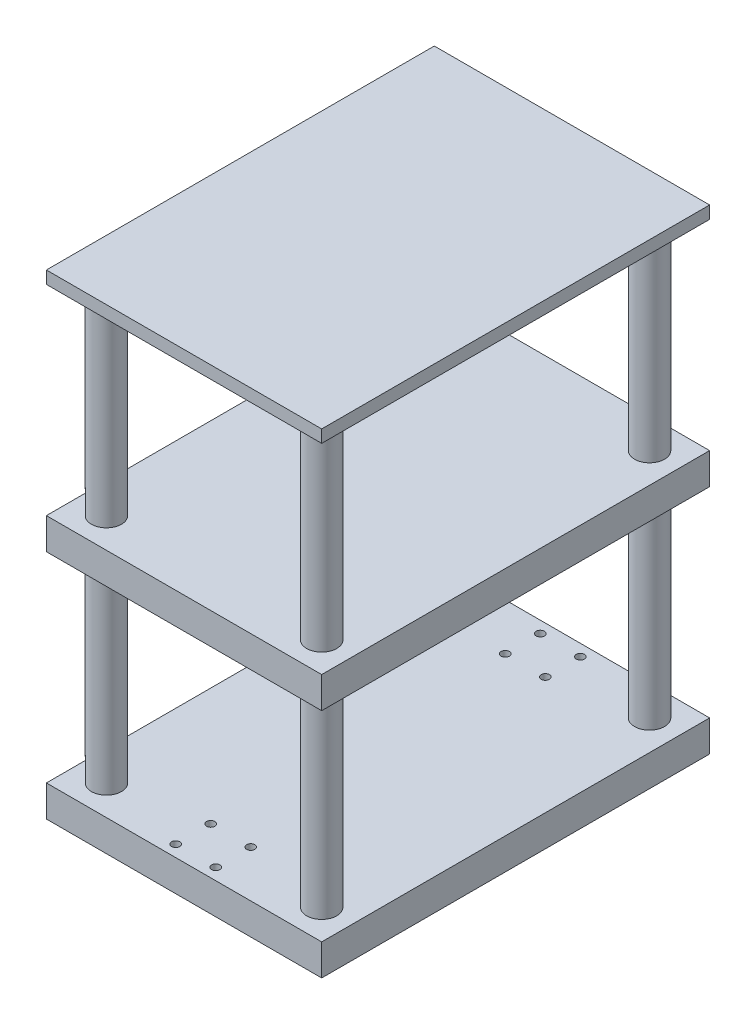
SolidWorks part; units mm, degrees
material "Custom Plastic"
ref_plane "Front Plane" through (0, 0, 0) normal (0, 0, 1) x (1, 0, 0)
ref_plane "Top Plane" through (0, 0, 0) normal (0, 1, 0) x (1, 0, 0)
ref_plane "Right Plane" through (0, 0, 0) normal (1, 0, 0) x (0, 0, -1)
sketch "Sketch1" plane through (0, 0, 0) normal (0, 1, 0) x (1, 0, 0)
  line L1 (-55, 77.5) -> (55, 77.5)
  line L2 (-55, 77.5) -> (-55, -77.5)
  line L3 (-55, -77.5) -> (55, -77.5)
  line L4 (55, 77.5) -> (55, -77.5)
  line L5 (-55, 77.5) -> (55, -77.5) construction
  line L6 (-55, -77.5) -> (55, 77.5) construction
  point P0 (0, 0)
  dimension "D1" = 155
  dimension "D2" = 110
extrude "Boss-Extrude1" add sketch "Sketch1" along normal blind 12.5
sketch "Sketch2" plane through (0, 12.5, 0) normal (0, 1, 0) x (1, 0, 0)
  line L0 (-55, 77.5) -> (-55, -77.5) construction
  line L1 (55, 77.5) -> (-55, 77.5) construction
  line L2 (0, 0) -> (73.1979, 0) construction
  circle A0 centre (-43, 65.5) radius 6
  dimension "D1" = 12
  dimension "D2" = 12
  dimension "D3" = 12
extrude "Boss-Extrude2" add sketch "Sketch2" along normal blind 80 contours A0
mirror "Mirror1" about plane through (0, 0, 0) normal (0, 0, 1) of "Boss-Extrude2"
mirror "Mirror2" about plane through (0, 0, 0) normal (1, 0, 0) of "Mirror1", "Boss-Extrude2"
ref_plane "Plane1" through (0, 92.5, 0) normal (0, 1, 0) x (1, 0, 0)
pattern_linear "LPattern1" count 2 spacing 92.5 along (0, -1, 0) of bodies 104
pattern_linear "LPattern2" [suppressed] count 2 spacing 92.5
sketch "Sketch4" plane through (0, -92.5, 0) normal (0, -1, 0) x (1, 0, 0)
  line L0 (0, 77.5) -> (0, 74.5)
  line L1 (-55, 77.5) -> (55, 77.5) construction
  line L2 (-13.25, 74.5) -> (13.25, 74.5)
  line L4 (-13.25, 74.5) -> (-13.25, 72.85)
  line L5 (-13.25, 72.85) -> (13.25, 72.85)
  line L6 (13.25, 72.85) -> (13.25, 74.5)
  circle A0 centre (-8, 72.85) radius 1.65
  circle A1 centre (8, 72.85) radius 1.65
  dimension "D1" = 3.3
  dimension "D2" = 3.3
  dimension "D3" = 16
  dimension "D4" = 26.5
  dimension "D5" = 5.25
  dimension "D6" = 5.25
  dimension "D7" = 1.65
  dimension "D8" = 3
sketch "Sketch5" plane through (0, -92.5, 0) normal (0, -1, 0) x (-1, 0, 0)
  point P0 (-8, -72.85)
  point P3 (8, -72.85)
hole_wizard "Ø3.3 (3.3) Diameter Hole1" positions "Sketch5" profile "Sketch6" hole size "Ø3.3" standard "ISO"
sketch "Sketch6" plane through (8, -92.5, 72.85) normal (1, 0, 0) x (0, 0, -1)
  line L0 (0, 0) -> (0, 20.9914)
  line L1 (0, 20.9914) -> (1.65, 20)
  line L2 (1.65, 20) -> (1.65, 0)
  line L5 (1.65, 0) -> (0, 0)
  line L10 (0, 20.9914) -> (-1.65, 20) construction
  line L11 (0, -6.35) -> (0, 107.95) construction
  dimension "Hole Dia." = 3.3
  dimension "Hole Depth" = 20
  dimension "Drill Angle" = 118
pattern_linear "LPattern3" count 2 spacing 14 along (0, 0, -1) of "Ø3.3 (3.3) Diameter Hole1"
mirror "Mirror3" about plane through (0, 0, 0) normal (0, 0, 1) of "LPattern3", "Ø3.3 (3.3) Diameter Hole1"
sketch "Sketch7" plane through (0, 92.5, 0) normal (0, 1, 0) x (1, 0, 0)
  line L4 (55, -77.5) -> (55, 77.5)
  line L5 (55, 77.5) -> (-55, 77.5)
  line L6 (-55, 77.5) -> (-55, -77.5)
  line L7 (-55, -77.5) -> (55, -77.5)
  line L8 (55, -77.5) -> (55, 77.5)
  line L9 (55, 77.5) -> (-55, 77.5)
  line L10 (-55, 77.5) -> (-55, -77.5)
  line L11 (-55, -77.5) -> (55, -77.5)
  dimension "D2" = 0
extrude "Boss-Extrude3" add sketch "Sketch7" along normal blind 5
